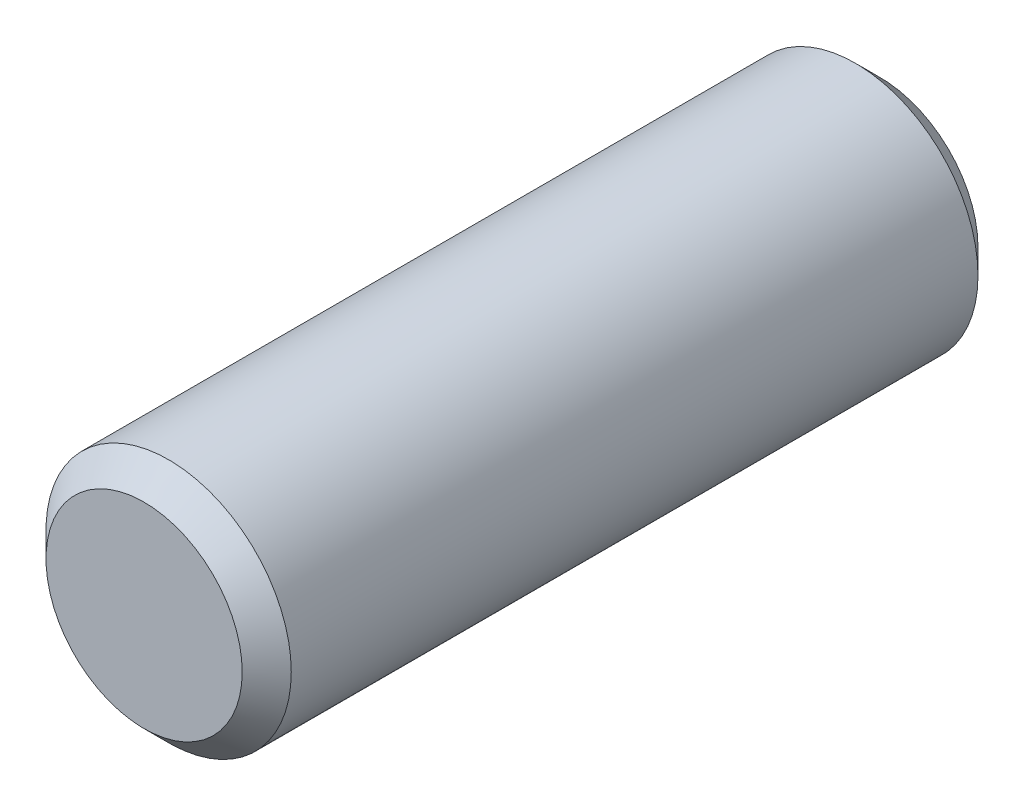
SolidWorks part; units mm, degrees
ref_plane "前视基准面" through (0, 0, 0) normal (0, 0, 1) x (1, 0, 0)
ref_plane "上视基准面" through (0, 0, 0) normal (0, 1, 0) x (1, 0, 0)
ref_plane "右视基准面" through (0, 0, 0) normal (1, 0, 0) x (0, 0, -1)
sketch "草图1" plane through (0, 0, 0) normal (0, 0, 1) x (1, 0, 0)
  circle A0 centre (0, 0) radius 1
  dimension "D1" = 2
extrude "凸台-拉伸1" add sketch "草图1" along normal mid plane 6
chamfer "倒角1" distance 0.2 angle 45 2 edges at (1, 0, -3) (1, 0, 3)
